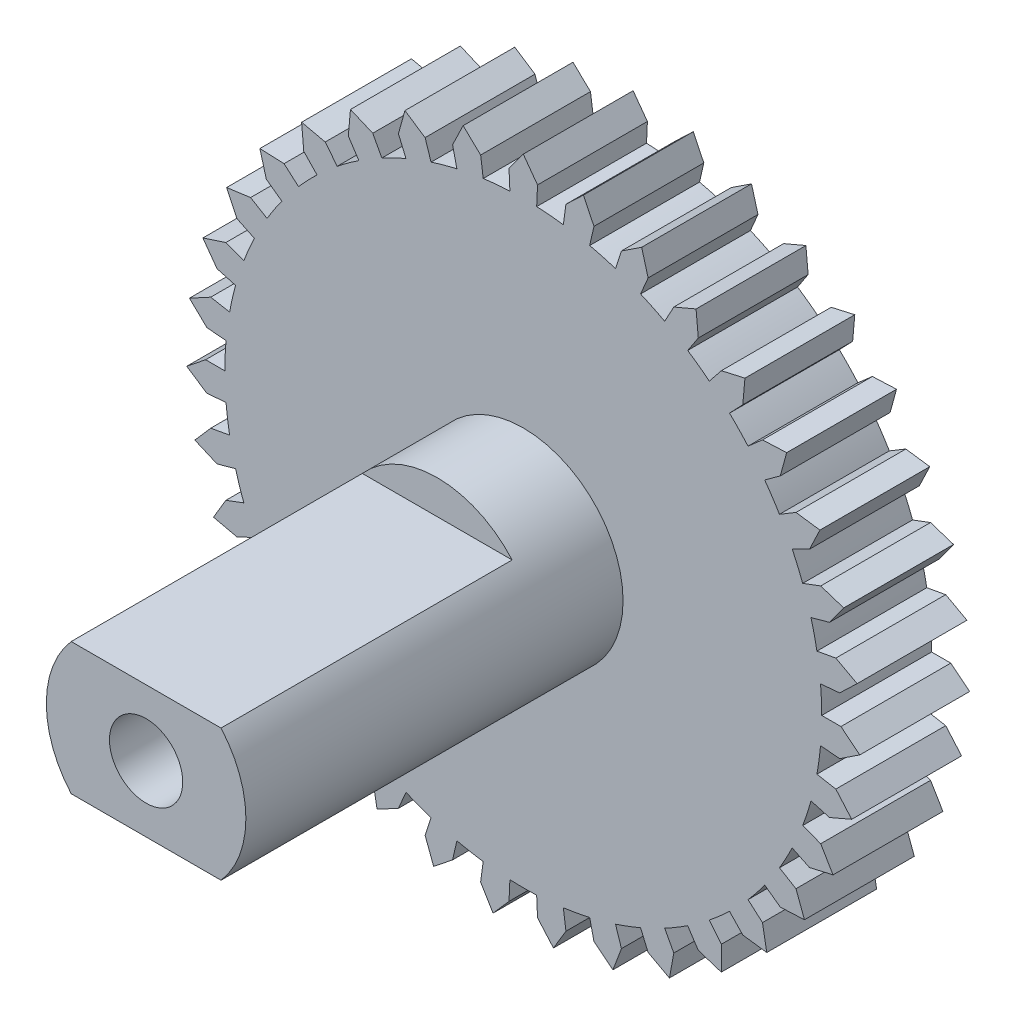
SolidWorks part; units mm, degrees
ref_plane "Front Plane" through (0, 0, 0) normal (0, 0, 1) x (1, 0, 0)
ref_plane "Top Plane" through (0, 0, 0) normal (0, 1, 0) x (1, 0, 0)
ref_plane "Right Plane" through (0, 0, 0) normal (1, 0, 0) x (0, 0, -1)
sketch "Sketch1" plane through (0, 0, 0) normal (0, 0, 1) x (1, 0, 0)
  line L0 (1.6427, 9.0522) -> (1.9304, 8.4575)
  line L1 (0, 9.2) -> (0.3892, 8.6663)
  line L2 (-0.3656, 8.1418) -> (-0.3892, 8.6663)
  line L3 (0, 9.2) -> (-0.3892, 8.6663)
  line L4 (0.3656, 8.1418) -> (0.3892, 8.6663)
  line L5 (1.094, 8.0762) -> (1.1645, 8.5965)
  line L6 (1.6427, 9.0522) -> (1.1645, 8.5965)
  line L7 (1.8135, 7.9457) -> (1.9304, 8.4575)
  line L8 (3.2326, 8.6134) -> (3.4095, 7.9769)
  line L9 (2.5185, 7.7511) -> (2.6807, 8.2504)
  line L10 (3.2326, 8.6134) -> (2.6807, 8.2504)
  line L11 (3.2032, 7.4942) -> (3.4095, 7.9769)
  line L12 (4.7187, 7.8977) -> (4.779, 7.2399)
  line L13 (3.862, 7.1769) -> (4.1108, 7.6392)
  line L14 (4.7187, 7.8977) -> (4.1108, 7.6392)
  line L15 (4.4898, 6.8018) -> (4.779, 7.2399)
  line L16 (6.053, 6.9283) -> (5.995, 6.2702)
  line L17 (5.0814, 6.3719) -> (5.4088, 6.7824)
  line L18 (6.053, 6.9283) -> (5.4088, 6.7824)
  line L19 (5.6322, 5.8908) -> (5.995, 6.2702)
  line L20 (7.1928, 5.7361) -> (7.0182, 5.099)
  line L21 (6.1375, 5.3622) -> (6.5329, 5.7076)
  line L22 (7.1928, 5.7361) -> (6.5329, 5.7076)
  line L23 (6.5935, 4.7904) -> (7.0182, 5.099)
  line L24 (8.1015, 4.3596) -> (7.8159, 3.7639)
  line L25 (6.9964, 4.1801) -> (7.447, 4.4494)
  line L26 (8.1015, 4.3596) -> (7.447, 4.4494)
  line L27 (7.3429, 3.5362) -> (7.8159, 3.7639)
  line L28 (8.7497, 2.843) -> (8.3624, 2.3079)
  line L29 (7.6303, 2.8637) -> (8.1218, 3.0482)
  line L30 (8.7497, 2.843) -> (8.1218, 3.0482)
  line L31 (7.8563, 2.1682) -> (8.3624, 2.3079)
  line L32 (9.1167, 1.2349) -> (8.6401, 0.7776)
  line L33 (8.019, 1.4552) -> (8.5356, 1.549)
  line L34 (9.1167, 1.2349) -> (8.5356, 1.549)
  line L35 (8.1172, 0.7306) -> (8.6401, 0.7776)
  line L36 (9.1907, -0.4128) -> (8.6401, -0.7776)
  line L37 (8.15, 0) -> (8.675, 0)
  line L38 (9.1907, -0.4128) -> (8.675, 0)
  line L39 (8.1172, -0.7306) -> (8.6401, -0.7776)
  line L40 (8.9693, -2.0472) -> (8.3624, -2.3079)
  line L41 (8.019, -1.4552) -> (8.5356, -1.549)
  line L42 (8.9693, -2.0472) -> (8.5356, -1.549)
  line L43 (7.8563, -2.1682) -> (8.3624, -2.3079)
  line L44 (8.4597, -3.6158) -> (7.8159, -3.7639)
  line L45 (7.6303, -2.8637) -> (8.1218, -3.0482)
  line L46 (8.4597, -3.6158) -> (8.1218, -3.0482)
  line L47 (7.3429, -3.5362) -> (7.8159, -3.7639)
  line L48 (7.6781, -5.0683) -> (7.0182, -5.099)
  line L49 (6.9964, -4.1801) -> (7.447, -4.4494)
  line L50 (7.6781, -5.0683) -> (7.447, -4.4494)
  line L51 (6.5935, -4.7904) -> (7.0182, -5.099)
  line L52 (6.6497, -6.3578) -> (5.995, -6.2702)
  line L53 (6.1375, -5.3622) -> (6.5329, -5.7076)
  line L54 (6.6497, -6.3578) -> (6.5329, -5.7076)
  line L55 (5.6322, -5.8908) -> (5.995, -6.2702)
  line L56 (5.4076, -7.443) -> (4.779, -7.2399)
  line L57 (5.0814, -6.3719) -> (5.4088, -6.7824)
  line L58 (5.4076, -7.443) -> (5.4088, -6.7824)
  line L59 (4.4898, -6.8018) -> (4.779, -7.2399)
  line L60 (3.9917, -8.2889) -> (3.4095, -7.9769)
  line L61 (3.862, -7.1769) -> (4.1108, -7.6392)
  line L62 (3.9917, -8.2889) -> (4.1108, -7.6392)
  line L63 (3.2032, -7.4942) -> (3.4095, -7.9769)
  line L64 (2.4475, -8.8685) -> (1.9304, -8.4575)
  line L65 (2.5185, -7.7511) -> (2.6807, -8.2504)
  line L66 (2.4475, -8.8685) -> (2.6807, -8.2504)
  line L67 (1.8135, -7.9457) -> (1.9304, -8.4575)
  line L68 (0.8247, -9.163) -> (0.3892, -8.6663)
  line L69 (1.094, -8.0762) -> (1.1645, -8.5965)
  line L70 (0.8247, -9.163) -> (1.1645, -8.5965)
  line L71 (0.3656, -8.1418) -> (0.3892, -8.6663)
  line L72 (-0.8247, -9.163) -> (-1.1645, -8.5965)
  line L73 (-0.3656, -8.1418) -> (-0.3892, -8.6663)
  line L74 (-0.8247, -9.163) -> (-0.3892, -8.6663)
  line L75 (-1.094, -8.0762) -> (-1.1645, -8.5965)
  line L76 (-2.4475, -8.8685) -> (-2.6807, -8.2504)
  line L77 (-1.8135, -7.9457) -> (-1.9304, -8.4575)
  line L78 (-2.4475, -8.8685) -> (-1.9304, -8.4575)
  line L79 (-2.5185, -7.7511) -> (-2.6807, -8.2504)
  line L80 (-3.9917, -8.2889) -> (-4.1108, -7.6392)
  line L81 (-3.2032, -7.4942) -> (-3.4095, -7.9769)
  line L82 (-3.9917, -8.2889) -> (-3.4095, -7.9769)
  line L83 (-3.862, -7.1769) -> (-4.1108, -7.6392)
  line L84 (-5.4076, -7.443) -> (-5.4088, -6.7824)
  line L85 (-4.4898, -6.8018) -> (-4.779, -7.2399)
  line L86 (-5.4076, -7.443) -> (-4.779, -7.2399)
  line L87 (-5.0814, -6.3719) -> (-5.4088, -6.7824)
  line L88 (-6.6497, -6.3578) -> (-6.5329, -5.7076)
  line L89 (-5.6322, -5.8908) -> (-5.995, -6.2702)
  line L90 (-6.6497, -6.3578) -> (-5.995, -6.2702)
  line L91 (-6.1375, -5.3622) -> (-6.5329, -5.7076)
  line L92 (-7.6781, -5.0683) -> (-7.447, -4.4494)
  line L93 (-6.5935, -4.7904) -> (-7.0182, -5.099)
  line L94 (-7.6781, -5.0683) -> (-7.0182, -5.099)
  line L95 (-6.9964, -4.1801) -> (-7.447, -4.4494)
  line L96 (-8.4597, -3.6158) -> (-8.1218, -3.0482)
  line L97 (-7.3429, -3.5362) -> (-7.8159, -3.7639)
  line L98 (-8.4597, -3.6158) -> (-7.8159, -3.7639)
  line L99 (-7.6303, -2.8637) -> (-8.1218, -3.0482)
  line L100 (-8.9693, -2.0472) -> (-8.5356, -1.549)
  line L101 (-7.8563, -2.1682) -> (-8.3624, -2.3079)
  line L102 (-8.9693, -2.0472) -> (-8.3624, -2.3079)
  line L103 (-8.019, -1.4552) -> (-8.5356, -1.549)
  line L104 (-9.1907, -0.4128) -> (-8.675, 0)
  line L105 (-8.1172, -0.7306) -> (-8.6401, -0.7776)
  line L106 (-9.1907, -0.4128) -> (-8.6401, -0.7776)
  line L107 (-8.15, 0) -> (-8.675, 0)
  line L108 (-9.1167, 1.2349) -> (-8.5356, 1.549)
  line L109 (-8.1172, 0.7306) -> (-8.6401, 0.7776)
  line L110 (-9.1167, 1.2349) -> (-8.6401, 0.7776)
  line L111 (-8.019, 1.4552) -> (-8.5356, 1.549)
  line L112 (-8.7497, 2.843) -> (-8.1218, 3.0482)
  line L113 (-7.8563, 2.1682) -> (-8.3624, 2.3079)
  line L114 (-8.7497, 2.843) -> (-8.3624, 2.3079)
  line L115 (-7.6303, 2.8637) -> (-8.1218, 3.0482)
  line L116 (-8.1015, 4.3596) -> (-7.447, 4.4494)
  line L117 (-7.3429, 3.5362) -> (-7.8159, 3.7639)
  line L118 (-8.1015, 4.3596) -> (-7.8159, 3.7639)
  line L119 (-6.9964, 4.1801) -> (-7.447, 4.4494)
  line L120 (-7.1928, 5.7361) -> (-6.5329, 5.7076)
  line L121 (-6.5935, 4.7904) -> (-7.0182, 5.099)
  line L122 (-7.1928, 5.7361) -> (-7.0182, 5.099)
  line L123 (-6.1375, 5.3622) -> (-6.5329, 5.7076)
  line L124 (-6.053, 6.9283) -> (-5.4088, 6.7824)
  line L125 (-5.6322, 5.8908) -> (-5.995, 6.2702)
  line L126 (-6.053, 6.9283) -> (-5.995, 6.2702)
  line L127 (-5.0814, 6.3719) -> (-5.4088, 6.7824)
  line L128 (-4.7187, 7.8977) -> (-4.1108, 7.6392)
  line L129 (-4.4898, 6.8018) -> (-4.779, 7.2399)
  line L130 (-4.7187, 7.8977) -> (-4.779, 7.2399)
  line L131 (-3.862, 7.1769) -> (-4.1108, 7.6392)
  line L132 (-3.2326, 8.6134) -> (-2.6807, 8.2504)
  line L133 (-3.2032, 7.4942) -> (-3.4095, 7.9769)
  line L134 (-3.2326, 8.6134) -> (-3.4095, 7.9769)
  line L135 (-2.5185, 7.7511) -> (-2.6807, 8.2504)
  line L136 (-1.6427, 9.0522) -> (-1.1645, 8.5965)
  line L137 (-1.8135, 7.9457) -> (-1.9304, 8.4575)
  line L138 (-1.6427, 9.0522) -> (-1.9304, 8.4575)
  line L139 (-1.094, 8.0762) -> (-1.1645, 8.5965)
  arc A0 (0.3656, 8.1418) -> (0.7306, 8.1172) centre (0, 0) cw
  arc A1 (-0.3656, 8.1418) -> (-0.7306, 8.1172) centre (0, 0) ccw
  arc A2 (1.8135, 7.9457) -> (2.1682, 7.8563) centre (0, 0) cw
  arc A3 (1.094, 8.0762) -> (0.7306, 8.1172) centre (0, 0) ccw
  arc A4 (3.2032, 7.4942) -> (3.5362, 7.3429) centre (0, 0) cw
  arc A5 (2.5185, 7.7511) -> (2.1682, 7.8563) centre (0, 0) ccw
  arc A6 (4.4898, 6.8018) -> (4.7904, 6.5935) centre (0, 0) cw
  arc A7 (3.862, 7.1769) -> (3.5362, 7.3429) centre (0, 0) ccw
  arc A8 (5.6322, 5.8908) -> (5.8908, 5.6322) centre (0, 0) cw
  arc A9 (5.0814, 6.3719) -> (4.7904, 6.5935) centre (0, 0) ccw
  arc A10 (6.5935, 4.7904) -> (6.8018, 4.4898) centre (0, 0) cw
  arc A11 (6.1375, 5.3622) -> (5.8908, 5.6322) centre (0, 0) ccw
  arc A12 (7.3429, 3.5362) -> (7.4942, 3.2032) centre (0, 0) cw
  arc A13 (6.9964, 4.1801) -> (6.8018, 4.4898) centre (0, 0) ccw
  arc A14 (7.8563, 2.1682) -> (7.9457, 1.8135) centre (0, 0) cw
  arc A15 (7.6303, 2.8637) -> (7.4942, 3.2032) centre (0, 0) ccw
  arc A16 (8.1172, 0.7306) -> (8.1418, 0.3656) centre (0, 0) cw
  arc A17 (8.019, 1.4552) -> (7.9457, 1.8135) centre (0, 0) ccw
  arc A18 (8.1172, -0.7306) -> (8.0762, -1.094) centre (0, 0) cw
  arc A19 (8.15, 0) -> (8.1418, 0.3656) centre (0, 0) ccw
  arc A20 (7.8563, -2.1682) -> (7.7511, -2.5185) centre (0, 0) cw
  arc A21 (8.019, -1.4552) -> (8.0762, -1.094) centre (0, 0) ccw
  arc A22 (7.3429, -3.5362) -> (7.1769, -3.862) centre (0, 0) cw
  arc A23 (7.6303, -2.8637) -> (7.7511, -2.5185) centre (0, 0) ccw
  arc A24 (6.5935, -4.7904) -> (6.3719, -5.0814) centre (0, 0) cw
  arc A25 (6.9964, -4.1801) -> (7.1769, -3.862) centre (0, 0) ccw
  arc A26 (5.6322, -5.8908) -> (5.3622, -6.1375) centre (0, 0) cw
  arc A27 (6.1375, -5.3622) -> (6.3719, -5.0814) centre (0, 0) ccw
  arc A28 (4.4898, -6.8018) -> (4.1801, -6.9964) centre (0, 0) cw
  arc A29 (5.0814, -6.3719) -> (5.3622, -6.1375) centre (0, 0) ccw
  arc A30 (3.2032, -7.4942) -> (2.8637, -7.6303) centre (0, 0) cw
  arc A31 (3.862, -7.1769) -> (4.1801, -6.9964) centre (0, 0) ccw
  arc A32 (1.8135, -7.9457) -> (1.4552, -8.019) centre (0, 0) cw
  arc A33 (2.5185, -7.7511) -> (2.8637, -7.6303) centre (0, 0) ccw
  arc A34 (0.3656, -8.1418) -> (0, -8.15) centre (0, 0) cw
  arc A35 (1.094, -8.0762) -> (1.4552, -8.019) centre (0, 0) ccw
  arc A36 (-1.094, -8.0762) -> (-1.4552, -8.019) centre (0, 0) cw
  arc A37 (-0.3656, -8.1418) -> (0, -8.15) centre (0, 0) ccw
  arc A38 (-2.5185, -7.7511) -> (-2.8637, -7.6303) centre (0, 0) cw
  arc A39 (-1.8135, -7.9457) -> (-1.4552, -8.019) centre (0, 0) ccw
  arc A40 (-3.862, -7.1769) -> (-4.1801, -6.9964) centre (0, 0) cw
  arc A41 (-3.2032, -7.4942) -> (-2.8637, -7.6303) centre (0, 0) ccw
  arc A42 (-5.0814, -6.3719) -> (-5.3622, -6.1375) centre (0, 0) cw
  arc A43 (-4.4898, -6.8018) -> (-4.1801, -6.9964) centre (0, 0) ccw
  arc A44 (-6.1375, -5.3622) -> (-6.3719, -5.0814) centre (0, 0) cw
  arc A45 (-5.6322, -5.8908) -> (-5.3622, -6.1375) centre (0, 0) ccw
  arc A46 (-6.9964, -4.1801) -> (-7.1769, -3.862) centre (0, 0) cw
  arc A47 (-6.5935, -4.7904) -> (-6.3719, -5.0814) centre (0, 0) ccw
  arc A48 (-7.6303, -2.8637) -> (-7.7511, -2.5185) centre (0, 0) cw
  arc A49 (-7.3429, -3.5362) -> (-7.1769, -3.862) centre (0, 0) ccw
  arc A50 (-8.019, -1.4552) -> (-8.0762, -1.094) centre (0, 0) cw
  arc A51 (-7.8563, -2.1682) -> (-7.7511, -2.5185) centre (0, 0) ccw
  arc A52 (-8.15, 0) -> (-8.1418, 0.3656) centre (0, 0) cw
  arc A53 (-8.1172, -0.7306) -> (-8.0762, -1.094) centre (0, 0) ccw
  arc A54 (-8.019, 1.4552) -> (-7.9457, 1.8135) centre (0, 0) cw
  arc A55 (-8.1172, 0.7306) -> (-8.1418, 0.3656) centre (0, 0) ccw
  arc A56 (-7.6303, 2.8637) -> (-7.4942, 3.2032) centre (0, 0) cw
  arc A57 (-7.8563, 2.1682) -> (-7.9457, 1.8135) centre (0, 0) ccw
  arc A58 (-6.9964, 4.1801) -> (-6.8018, 4.4898) centre (0, 0) cw
  arc A59 (-7.3429, 3.5362) -> (-7.4942, 3.2032) centre (0, 0) ccw
  arc A60 (-6.1375, 5.3622) -> (-5.8908, 5.6322) centre (0, 0) cw
  arc A61 (-6.5935, 4.7904) -> (-6.8018, 4.4898) centre (0, 0) ccw
  arc A62 (-5.0814, 6.3719) -> (-4.7904, 6.5935) centre (0, 0) cw
  arc A63 (-5.6322, 5.8908) -> (-5.8908, 5.6322) centre (0, 0) ccw
  arc A64 (-3.862, 7.1769) -> (-3.5362, 7.3429) centre (0, 0) cw
  arc A65 (-4.4898, 6.8018) -> (-4.7904, 6.5935) centre (0, 0) ccw
  arc A66 (-2.5185, 7.7511) -> (-2.1682, 7.8563) centre (0, 0) cw
  arc A67 (-3.2032, 7.4942) -> (-3.5362, 7.3429) centre (0, 0) ccw
  arc A68 (-1.094, 8.0762) -> (-0.7306, 8.1172) centre (0, 0) cw
  arc A69 (-1.8135, 7.9457) -> (-2.1682, 7.8563) centre (0, 0) ccw
  circle A70 centre (0, 0) radius 1
  point P250 (0, 0)
  dimension "D1" = 35
  dimension "D2" = 16.3
  dimension "D3" = 2
extrude "Boss-Extrude1" add sketch "Sketch1" along normal blind 3
sketch "Sketch2" plane through (0, 0, 0) normal (0, 0, -1) x (-1, 0, 0)
  circle A0 centre (0, 0) radius 1.75
  circle A1 centre (0, 0) radius 1 construction
  circle A2 centre (0, 0) radius 1
  dimension "D1" = 3.5
extrude "Boss-Extrude2" add sketch "Sketch2" along normal blind 0.5
sketch "Sketch3" plane through (0, 0, 3) normal (0, 0, 1) x (1, 0, 0)
  circle A0 centre (0, 0) radius 2.725
  circle A2 centre (0, 0) radius 1
  dimension "D1" = 5.45
extrude "Boss-Extrude3" add sketch "Sketch3" along normal blind 10.3
sketch "Sketch4" plane through (0, 0, 13.3) normal (0, 0, 1) x (1, 0, 0)
  line L1 (-2.0459, -1.8) -> (2.0459, -1.8)
  line L3 (-2.0459, 1.8) -> (2.0459, 1.8)
  circle A0 centre (0, 0) radius 2.725 construction
  arc A1 (2.0459, 1.8) -> (-2.0459, 1.8) centre (0, 0) ccw
  arc A2 (-2.0459, -1.8) -> (2.0459, -1.8) centre (0, 0) ccw
  point P0 (0, 0)
extrude "Cut-Extrude1" cut sketch "Sketch4" against normal blind 7.95
